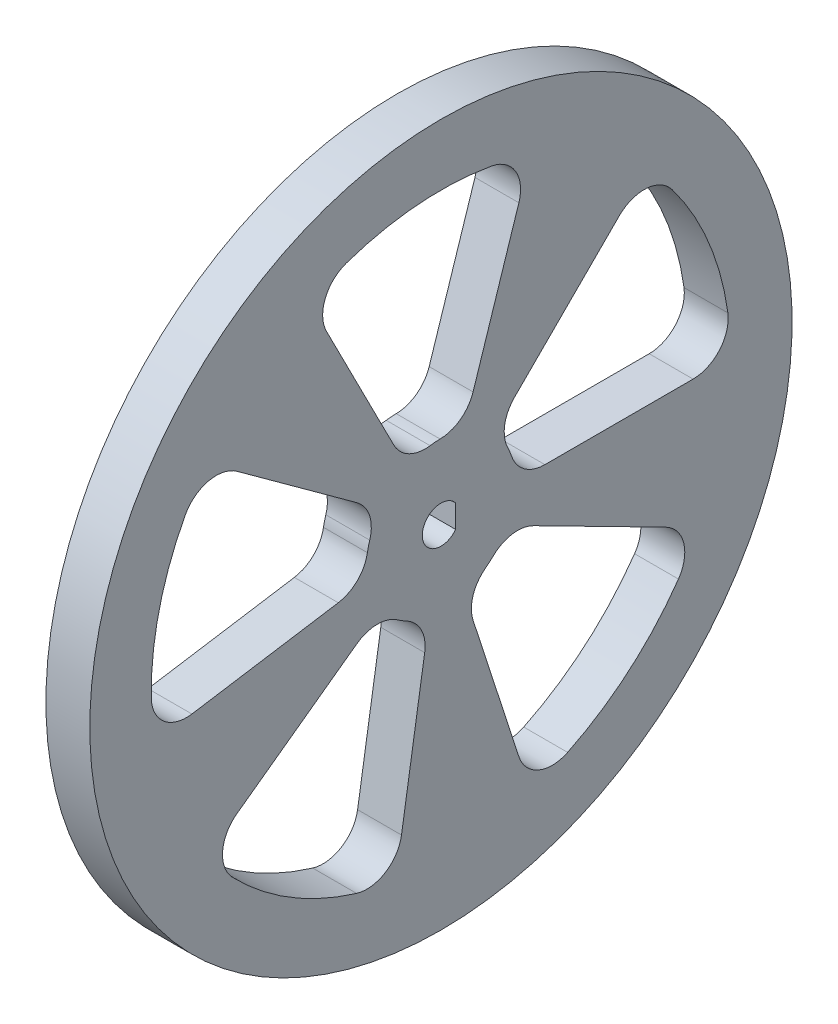
SolidWorks part; units mm, degrees
material "ABS"
ref_plane "Front Plane" through (0, 0, 0) normal (0, 0, 1) x (1, 0, 0)
ref_plane "Top Plane" through (0, 0, 0) normal (0, 1, 0) x (1, 0, 0)
ref_plane "Right Plane" through (0, 0, 0) normal (1, 0, 0) x (0, 0, -1)
sketch "Sketch3" plane through (0, 0, 0) normal (0, 0, 1) x (1, 0, 0)
  line L1 (-2.5, 0) -> (2.5, 0)
  line L5 (2.5, 0) -> (2.5, 40)
  line L6 (-2.5, 0) -> (-2.5, 40)
  line L12 (0, 0) -> (0, 43) construction
  line L20 (2.5, 40) -> (0, 40) construction
  line L21 (0, 40) -> (-2.5, 40) construction
  line L22 (-2.5, 40) -> (2.5, 40)
  dimension "D1" = 2.5
  dimension "D2" = 40
revolve "Shape_Roue" add sketch "Sketch3" angle 360 about L1
sketch "Sketch6" plane through (2.5, 0, 0) normal (1, 0, 0) x (0, 0, -1)
  line L0 (8.3741, 8.3741) -> (20.3101, 20.3101)
  line L1 (28.7228, 0) -> (11.8427, 0)
  line L2 (0, 0) -> (24.1309, 0) construction
  line L3 (0, 0) -> (0, 5.2799) construction
  line L4 (33, 0) -> (0, 0) construction
  line L5 (23.3345, 23.3345) -> (0, 0) construction
  line L6 (7.853, 3.2528) -> (0, 0) construction
  line L7 (7.853, 3.2528) -> (30.488, 12.6286) construction
  line L8 (30.488, 12.6286) -> (36.9552, 15.3073) construction
  arc A1 (8.3741, 8.3741) -> (7.6177, 3.771) centre (11.2025, 5.5456) ccw
  arc A2 (7.6177, 3.771) -> (8.053, 2.72) centre (0, 0) cw
  arc A3 (26.33, 19.8929) -> (32.6846, 4.5517) centre (0, 0) cw
  arc A5 (11.8427, 0) -> (8.053, 2.72) centre (11.8427, 4) cw
  arc A6 (28.7228, 0) -> (32.6846, 4.5517) centre (28.7228, 4) ccw
  arc A7 (20.3101, 20.3101) -> (26.33, 19.8929) centre (23.1385, 17.4817) cw
  circle A8 centre (0, 0) radius 40 construction
  point P5 (35.7461, 17.9504)
  dimension "D1" = 45
  dimension "D3" = 7
  dimension "D5" = 4
  dimension "D2" = 8.5
extrude "Cut-Extrude1" cut sketch "Sketch6" along direction (-1, 0, 0) on the side against the normal up to next (5 mm away)
pattern_circular "CirPattern1" count 5 over 360 about axis through (0, 0, 0) along (1, 0, 0) of "Cut-Extrude1"
sketch "Sketch8" plane through (-2.5, 0, 0) normal (1, 0, 0) x (0, 0, -1)
  line L0 (0, 0) -> (2.75, 0) construction
  circle A0 centre (0, 0) radius 2.75
  dimension "D1" = 2.75
extrude "Boss-Extrude1" add sketch "Sketch8" against normal blind 3
sketch "Sketch7" plane through (2.5, 0, 0) normal (1, 0, 0) x (0, 0, -1)
  line L0 (0, 0) -> (1.9231, 0) construction
  line L1 (0, -2.125) -> (0, 2.125) construction
  line L2 (0, 0) -> (-2.125, 0)
  line L3 (1.675, 1.3077) -> (1.675, -1.3077)
  arc A0 (1.675, 1.3077) -> (1.675, -1.3077) centre (0, 0) ccw
  dimension "D1" = 4.25
  dimension "D2" = 3.8
extrude "Cut-Extrude2" cut sketch "Sketch7" against normal up to next
